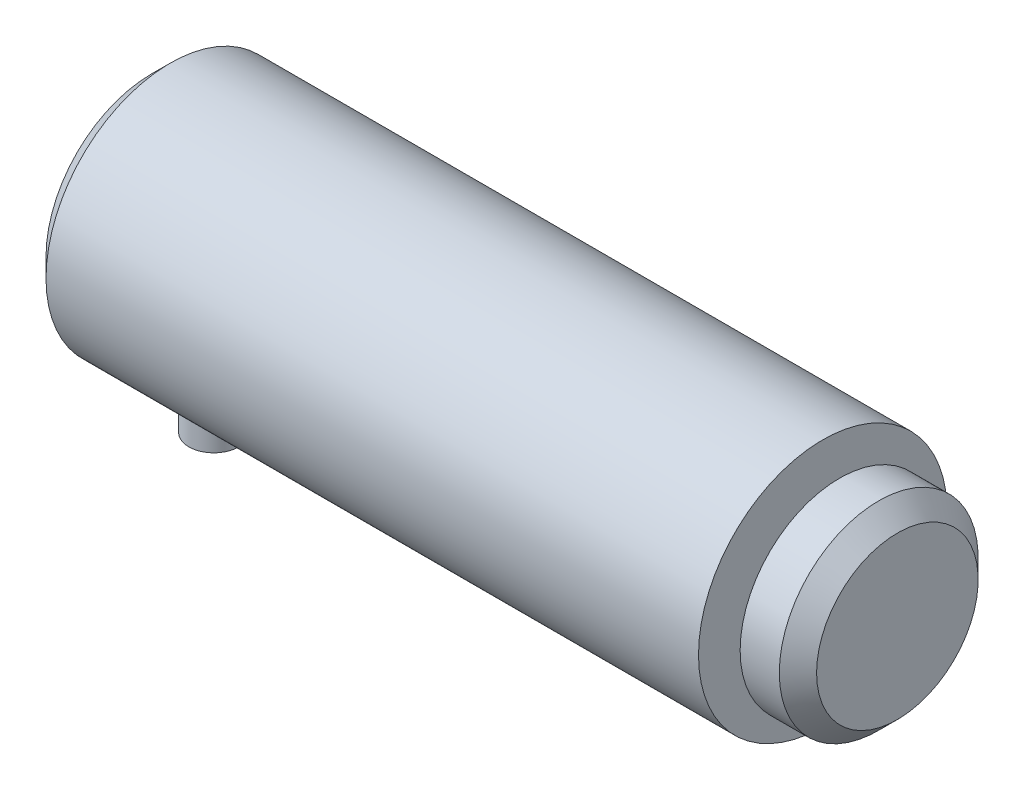
SolidWorks part; units mm, degrees
ref_plane "Front Plane" through (0, 0, 0) normal (0, 0, 1) x (1, 0, 0)
ref_plane "Top Plane" through (0, 0, 0) normal (0, 1, 0) x (1, 0, 0)
ref_plane "Right Plane" through (0, 0, 0) normal (1, 0, 0) x (0, 0, -1)
ref_plane "Plane1" through (0, 0, 0) normal (0, 0, 1) x (1, 0, 0)
sketch "Sketch1" plane through (0, 0, 0) normal (0, 0, 1) x (1, 0, 0)
  line L0 (-30, 0) -> (-30, 10)
  line L1 (-30, 10) -> (24, 10)
  line L2 (24, 10) -> (24, 0)
  line L3 (24, 0) -> (-30, 0)
  line L4 (24, 0) -> (-30, 0) construction
revolve "Revolve1" add sketch "Sketch1" angle 360 about L4
ref_plane "Plane2" through (0, 0, 0) normal (0, 0, 1) x (1, 0, 0)
sketch "Sketch2" plane through (0, 0, 0) normal (0, 0, 1) x (1, 0, 0)
  line L0 (-30, 8.5) -> (-28.5, 10)
  line L1 (-28.5, 10) -> (-30, 10)
  line L2 (-30, 10) -> (-30, 8.5)
  line L3 (49, 0) -> (-49, 0) construction
revolve "Cut-Revolve1" cut sketch "Sketch2" angle 360 about L3
ref_plane "Plane3" through (0, 0, 0) normal (0, 1, 0) x (1, 0, 0)
sketch "Sketch3" plane through (0, 0, 0) normal (0, 1, 0) x (1, 0, 0)
  circle A0 centre (-25, 0) radius 2
extrude "Boss-Extrude1" add sketch "Sketch3" against normal blind 14
ref_plane "Plane4" through (0, 0, 0) normal (0, 0, 1) x (1, 0, 0)
sketch "Sketch4" plane through (0, 0, 0) normal (0, 0, 1) x (1, 0, 0)
  line L0 (24, 0) -> (24, 8)
  line L1 (24, 8) -> (30, 8)
  line L2 (30, 8) -> (30, 0)
  line L3 (30, 0) -> (24, 0)
  line L4 (30, 0) -> (24, 0) construction
revolve "Revolve2" add sketch "Sketch4" angle 360 about L4
ref_plane "Plane5" through (0, 0, 0) normal (0, 0, 1) x (1, 0, 0)
sketch "Sketch5" plane through (0, 0, 0) normal (0, 0, 1) x (1, 0, 0)
  line L0 (24, 6) -> (25.35, 6)
  line L1 (25.35, 6) -> (25.35, 8)
  line L2 (25.35, 8) -> (24, 8)
  line L3 (24, 8) -> (24, 6)
  line L4 (49, 0) -> (-49, 0) construction
revolve "Cut-Revolve2" cut sketch "Sketch5" angle 360 about L4
ref_plane "Plane6" through (0, 0, 0) normal (0, 0, 1) x (1, 0, 0)
sketch "Sketch6" plane through (0, 0, 0) normal (0, 0, 1) x (1, 0, 0)
  line L0 (28.5, 8) -> (30, 6.5)
  line L1 (30, 6.5) -> (30, 8)
  line L2 (30, 8) -> (28.5, 8)
  line L3 (49, 0) -> (-49, 0) construction
revolve "Cut-Revolve3" cut sketch "Sketch6" angle 360 about L3
